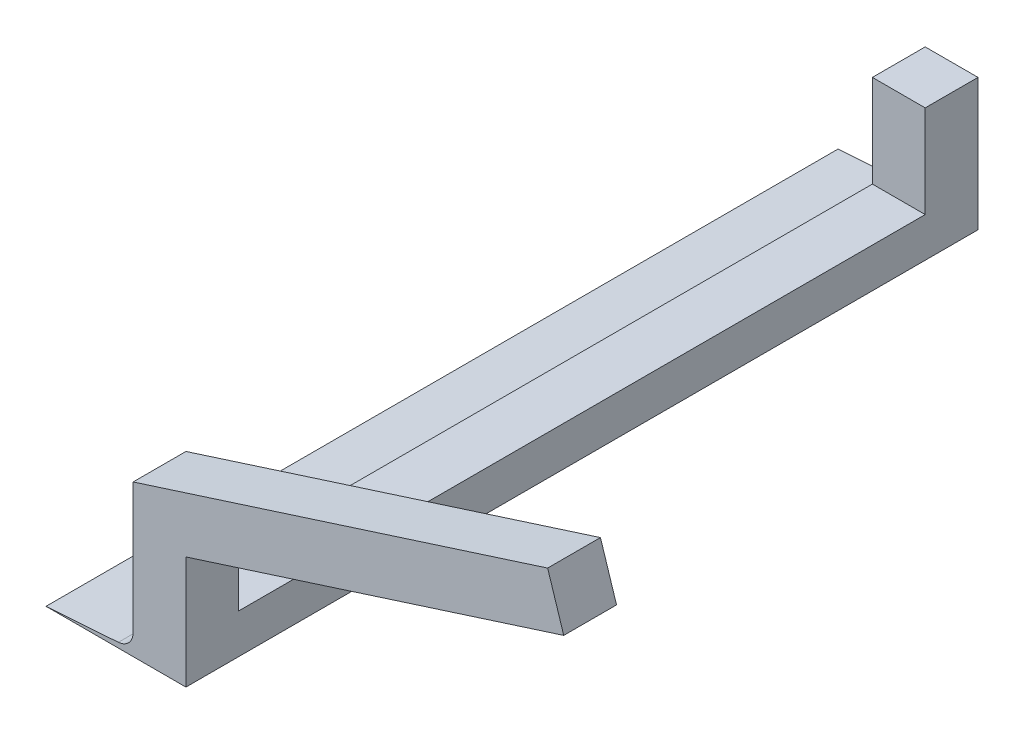
SolidWorks part; units mm, degrees
ref_plane "Plan de face" through (0, 0, 0) normal (0, 0, 1) x (1, 0, 0)
ref_plane "Plan de dessus" through (0, 0, 0) normal (0, 1, 0) x (1, 0, 0)
ref_plane "Plan de droite" through (0, 0, 0) normal (1, 0, 0) x (0, 0, -1)
sketch "Esquisse2" plane through (0, 0, 0) normal (0, 0, 1) x (1, 0, 0)
  line L0 (0, 0) -> (-35, 0)
  line L1 (-7.5837, 1.9069) -> (-35, 0)
  line L2 (0, 5.028) -> (0, 15)
  line L3 (0, 0) -> (0, 5.028)
  line L4 (0, 15) -> (-2, 15)
  line L5 (-2, 15) -> (-2, 7.8924)
  line L7 (0, 15) -> (18, 15)
  line L8 (0, 15) -> (0, 0)
  line L9 (0, 0) -> (18, 0)
  line L10 (18, 15) -> (18, 0)
  arc A0 (-2, 7.8924) -> (-7.5837, 1.9069) centre (-8, 7.8924) cw
  dimension "D3" = 6
  dimension "D1" = 35
  dimension "D2" = 2
  dimension "D4" = 15
  dimension "D5" = 18
extrude "Boss.-Extru.2" add sketch "Esquisse2" along normal blind 300 contours L10 L7 L2 L3 L9 | L5 A0 L1 L0 L3 L2 L4
sketch "Esquisse7" plane through (0, 15, 0) normal (0, 1, 0) x (1, 0, 0)
  line L0 (18, -300) -> (18, 0) construction
  line L1 (-2, 0) -> (18, 0)
  line L2 (-2, 0) -> (-2, -20)
  line L3 (-2, -20) -> (18, -20)
  line L4 (18, 0) -> (18, -20)
  line L5 (-2, -300) -> (-2, 0) construction
  line L6 (18, -300) -> (-2, -300)
  line L7 (18, -300) -> (18, -280)
  line L8 (18, -280) -> (-2, -280)
  line L9 (-2, -300) -> (-2, -280)
  dimension "D1" = 20
  dimension "D2" = 20
extrude "Boss.-Extru.5" add sketch "Esquisse7" along normal blind 35
sketch "Esquisse8" plane through (0, 0, 300) normal (0, 0, 1) x (1, 0, 0)
  line L0 (8, 50) -> (8, 89.1309) construction
  line L1 (-2, 50) -> (18, 50) construction
  line L2 (8, 50) -> (158.0492, 98.0311) construction
  line L3 (158.0492, 98.0311) -> (155.0006, 107.5551)
  line L4 (158.0492, 98.0311) -> (161.0979, 88.5072)
  line L5 (155.0006, 107.5551) -> (-2, 57.2988)
  line L6 (-2, 57.2988) -> (-2, 36.2991)
  line L7 (-2, 50) -> (-2, 7.8924) construction
  line L8 (-2, 36.2991) -> (161.0979, 88.5072)
  dimension "D1" = 17.75
  dimension "D2" = 10
  dimension "D3" = 10
extrude "Boss.-Extru.6" add sketch "Esquisse8" against normal up to surface (20 mm away) up to face at (8, 32.5, 280)
